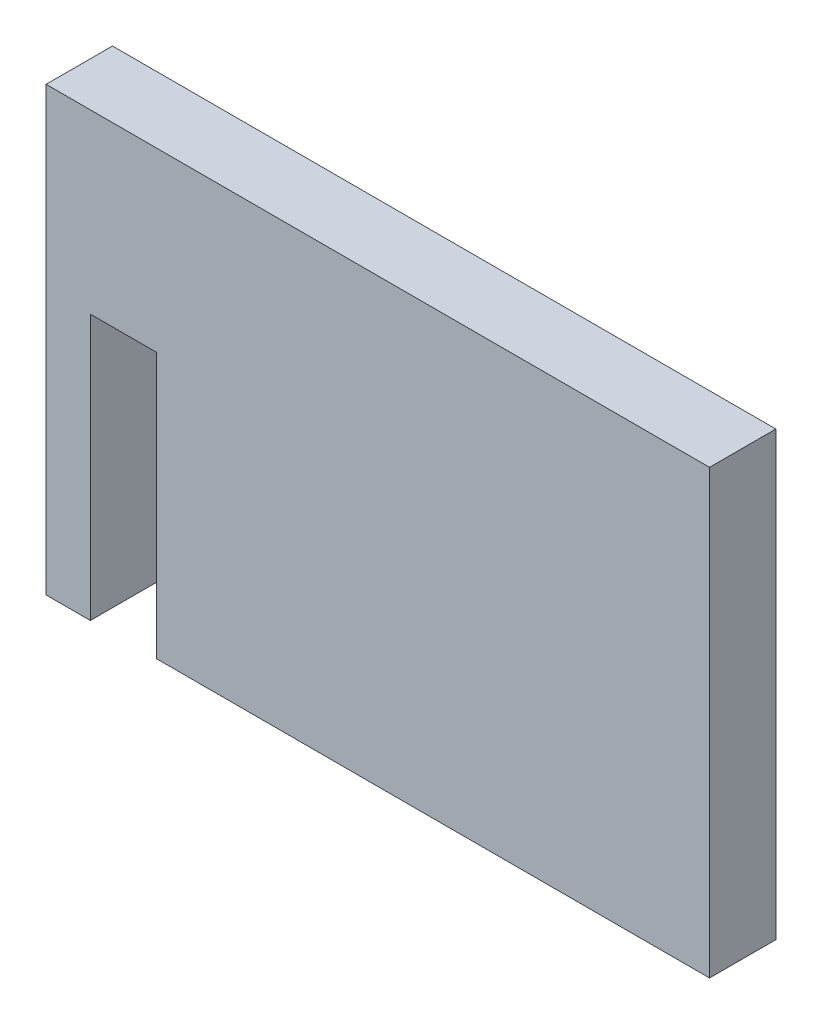
SolidWorks part; units mm, degrees
ref_plane "Front Plane" through (0, 0, 0) normal (0, 0, 1) x (1, 0, 0)
ref_plane "Top Plane" through (0, 0, 0) normal (0, 1, 0) x (1, 0, 0)
ref_plane "Right Plane" through (0, 0, 0) normal (1, 0, 0) x (0, 0, -1)
sketch "Sketch1" plane through (0, 0, 0) normal (0, 0, 1) x (1, 0, 0)
  line L0 (-11.9423, -10) -> (13.0577, -10)
  line L1 (-16.9423, 10) -> (13.0577, 10)
  line L2 (-16.9423, 10) -> (-16.9423, -10)
  line L3 (-16.9423, -10) -> (-14.9423, -10)
  line L4 (13.0577, 10) -> (13.0577, -10)
  line L7 (-14.9423, 2) -> (-11.9423, 2)
  line L8 (-14.9423, 2) -> (-14.9423, -10)
  line L10 (-11.9423, 2) -> (-11.9423, -10)
  point P0 (0, 0)
  point P6 (-13.5, -4)
  point P11 (0, 0)
  point P12 (0, 0)
  point P13 (0, 0)
  dimension "D1" = 20
  dimension "D2" = 30
extrude "Boss-Extrude1" add sketch "Sketch1" along normal blind 3
